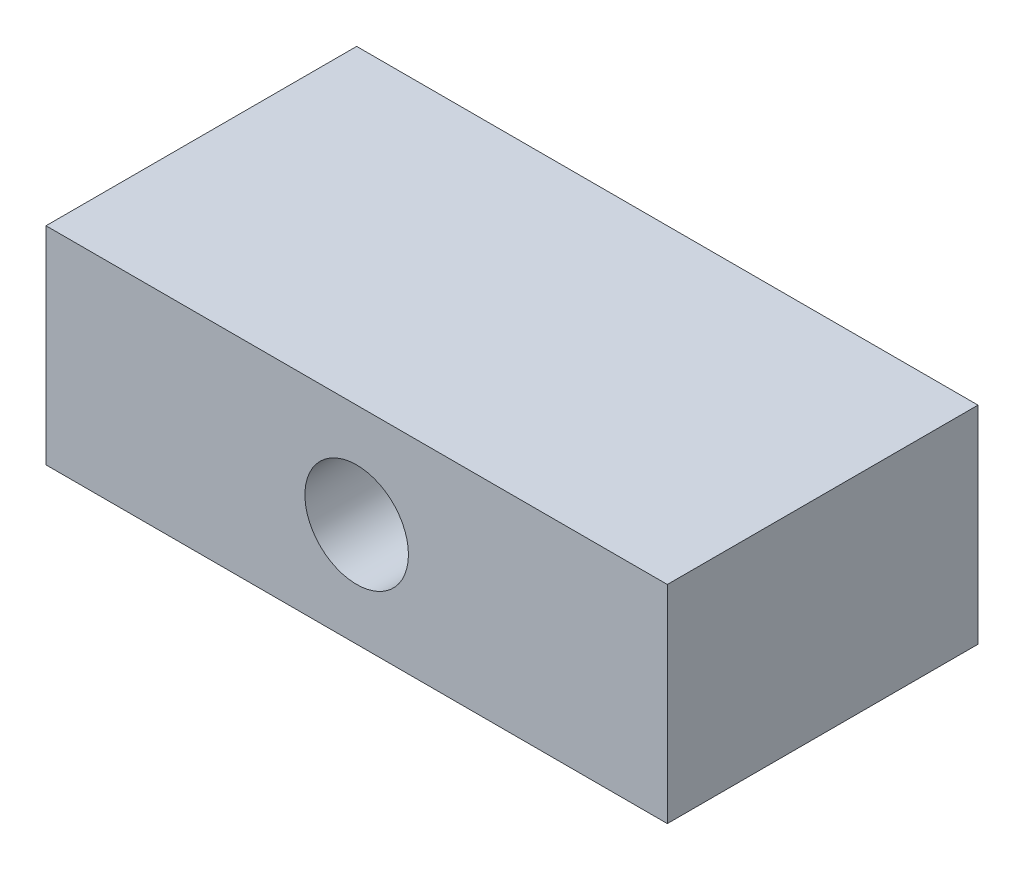
SolidWorks part; units mm, degrees
ref_plane "Piano frontale" through (0, 0, 0) normal (0, 0, 1) x (1, 0, 0)
ref_plane "Piano superiore" through (0, 0, 0) normal (0, 1, 0) x (1, 0, 0)
ref_plane "Piano destro" through (0, 0, 0) normal (1, 0, 0) x (0, 0, -1)
sketch "Sketch1" plane through (0, 0, 0) normal (0, 1, 0) x (1, 0, 0)
  line L1 (-150, -75) -> (150, -75)
  line L2 (-150, -75) -> (-150, 75)
  line L3 (-150, 75) -> (150, 75)
  line L4 (150, -75) -> (150, 75)
  line L5 (-150, -75) -> (150, 75) construction
  line L6 (-150, 75) -> (150, -75) construction
  point P0 (0, 0)
  dimension "D1" = 150
  dimension "D2" = 300
extrude "Boss-Extrude1" add sketch "Sketch1" along normal mid plane 100
sketch "Sketch2" plane through (0, 0, 75) normal (0, 0, 1) x (1, 0, 0)
  circle A0 centre (0, 0) radius 25
  dimension "D1" = 50
extrude "Cut-Extrude1" cut sketch "Sketch2" against normal through all
